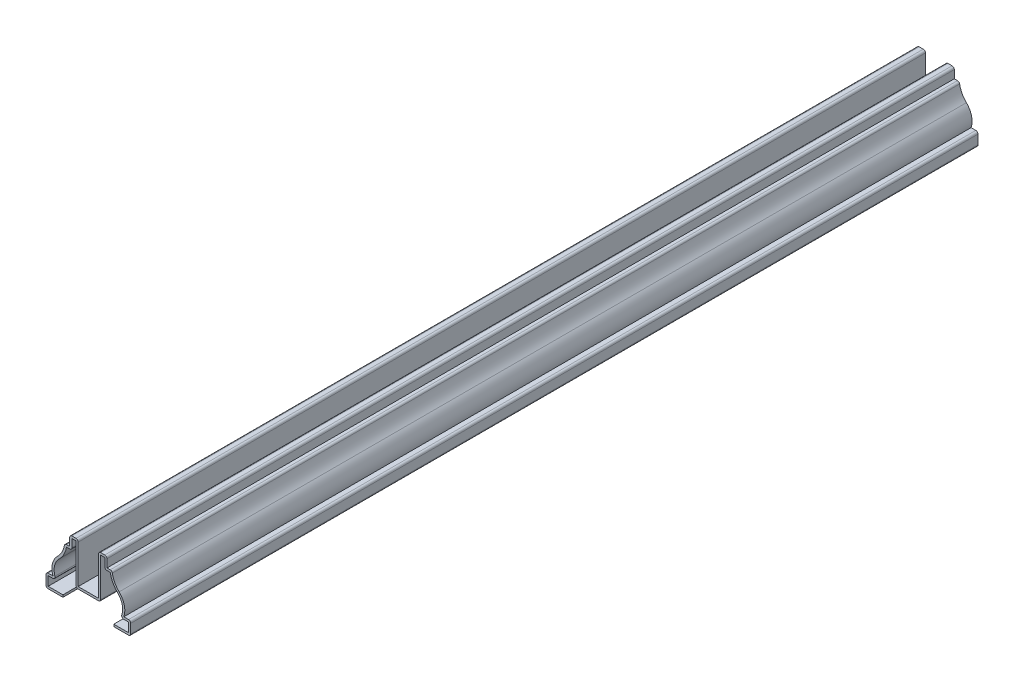
SolidWorks part; units mm, degrees
ref_plane "Front Plane" through (0, 0, 0) normal (0, 0, 1) x (1, 0, 0)
ref_plane "Top Plane" through (0, 0, 0) normal (0, 1, 0) x (1, 0, 0)
ref_plane "Right Plane" through (0, 0, 0) normal (1, 0, 0) x (0, 0, -1)
sketch "Sketch1" plane through (0, 0, 0) normal (0, 0, 1) x (1, 0, 0)
  line L0 (0, 0) -> (0, 23.1736) construction
  line L1 (-11.9062, 0) -> (-19.8438, 0)
  line L2 (-19.8438, 0) -> (-19.8438, 6.35)
  line L3 (-19.8438, 6.35) -> (-16.6119, 6.35)
  line L4 (-11.1125, 22.225) -> (-8.7313, 22.225)
  line L5 (-8.7313, 22.225) -> (-8.7313, 26.9875)
  line L6 (-8.7313, 26.9875) -> (-4.7625, 26.9875)
  line L7 (-4.7625, 26.9875) -> (-4.7625, 7.9375)
  line L8 (-4.7625, 7.9375) -> (4.7625, 7.9375)
  line L9 (4.7625, 26.9875) -> (4.7625, 7.9375)
  line L10 (8.7313, 26.9875) -> (4.7625, 26.9875)
  line L11 (8.7313, 22.225) -> (8.7313, 26.9875)
  line L12 (11.1125, 22.225) -> (8.7313, 22.225)
  line L13 (19.8438, 6.35) -> (16.6119, 6.35)
  line L14 (19.8438, 0) -> (19.8438, 6.35)
  line L15 (11.9062, 0) -> (19.8438, 0)
  arc A0 (-16.6119, 6.35) -> (-14.4209, 15.3883) centre (-8.3344, 9.1281) cw
  arc A1 (-14.4209, 15.3883) -> (-11.1125, 22.225) centre (-22.1673, 23.3557) ccw
  arc A2 (14.4209, 15.3883) -> (11.1125, 22.225) centre (22.1673, 23.3557) cw
  arc A3 (16.6119, 6.35) -> (14.4209, 15.3883) centre (8.3344, 9.1281) ccw
  point P16 (0, 0)
  point P17 (-13.4707, 22.225)
  point P18 (-17.106, 22.225)
  point P19 (-22.9335, 13.4129)
  point P20 (-13.9845, 8.4722)
  point P21 (-19.6143, 5.4664)
  point P22 (-17.106, 12.7507)
  point P23 (-17.9007, 14.5387)
  point P24 (-15.7683, 26.9875)
  point P31 (0, 7.9375)
extrude "Extrude-Thin1" add sketch "Sketch1" against normal blind 396.875 thin
fillet "Fillet1" radius 1.016 16 edges at (-15.0522, 5.334, -198.4375) (-19.8438, 0, -198.4375) (-19.8438, 6.35, -198.4375) (15.0522, 5.334, -198.4375) (19.8438, 0, -198.4375) (19.8438, 6.35, -198.4375) (5.7785, 6.9215, -198.4375) (-5.7785, 6.9215, -198.4375) (-11.1125, 22.225, -198.4375) (-7.7153, 21.209, -198.4375) (11.1125, 22.225, -198.4375) (7.7153, 21.209, -198.4375) (8.7313, 26.9875, -198.4375) (4.7625, 26.9875, -198.4375) (-4.7625, 26.9875, -198.4375) (-8.7313, 26.9875, -198.4375)
equation "\"D1@Extrude-Thin1\"=\"D14@Sketch1\"*10"
